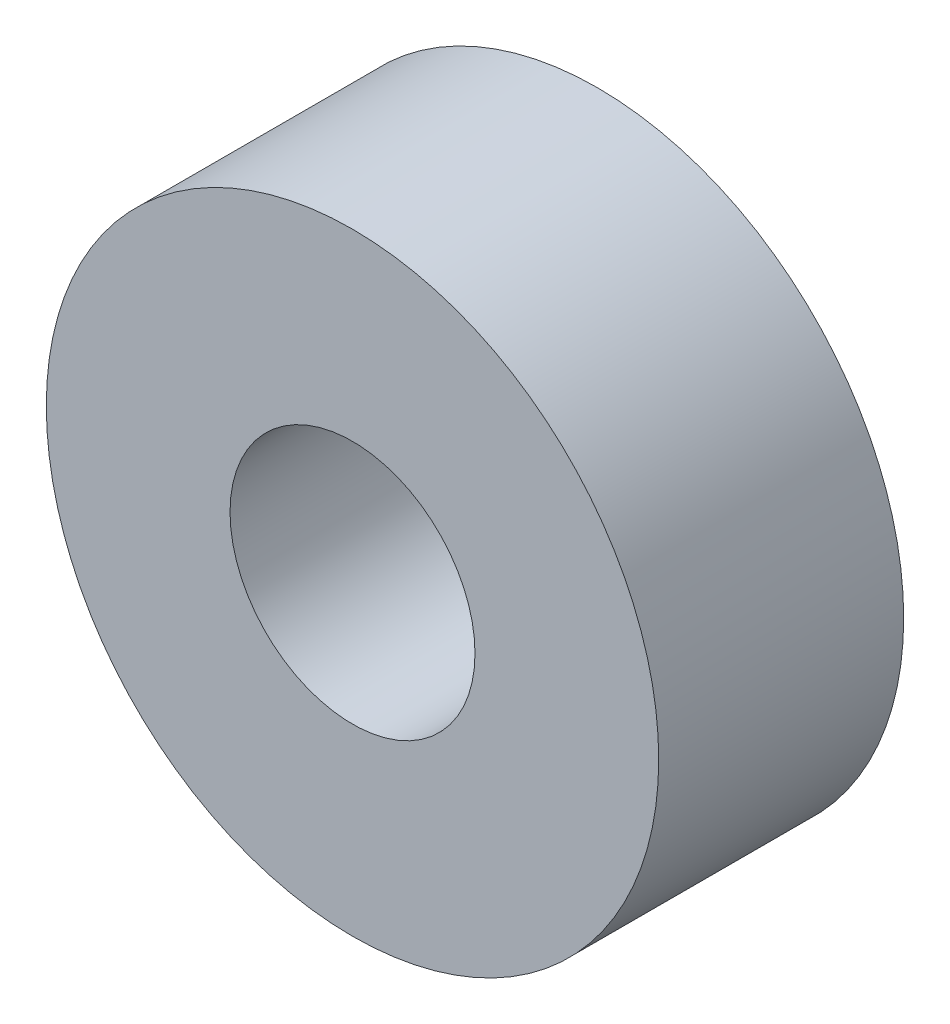
SolidWorks part; units mm, degrees
ref_plane "Front Plane" through (0, 0, 0) normal (0, 0, 1) x (1, 0, 0)
ref_plane "Top Plane" through (0, 0, 0) normal (0, 1, 0) x (1, 0, 0)
ref_plane "Right Plane" through (0, 0, 0) normal (1, 0, 0) x (0, 0, -1)
sketch "Sketch1" plane through (0, 0, 0) normal (0, 0, 1) x (1, 0, 0)
  circle A0 centre (0, 0) radius 5
  circle A1 centre (0, 0) radius 2
  dimension "D1" = 10
  dimension "D2" = 4
extrude "Boss-Extrude1" add sketch "Sketch1" along normal mid plane 4
